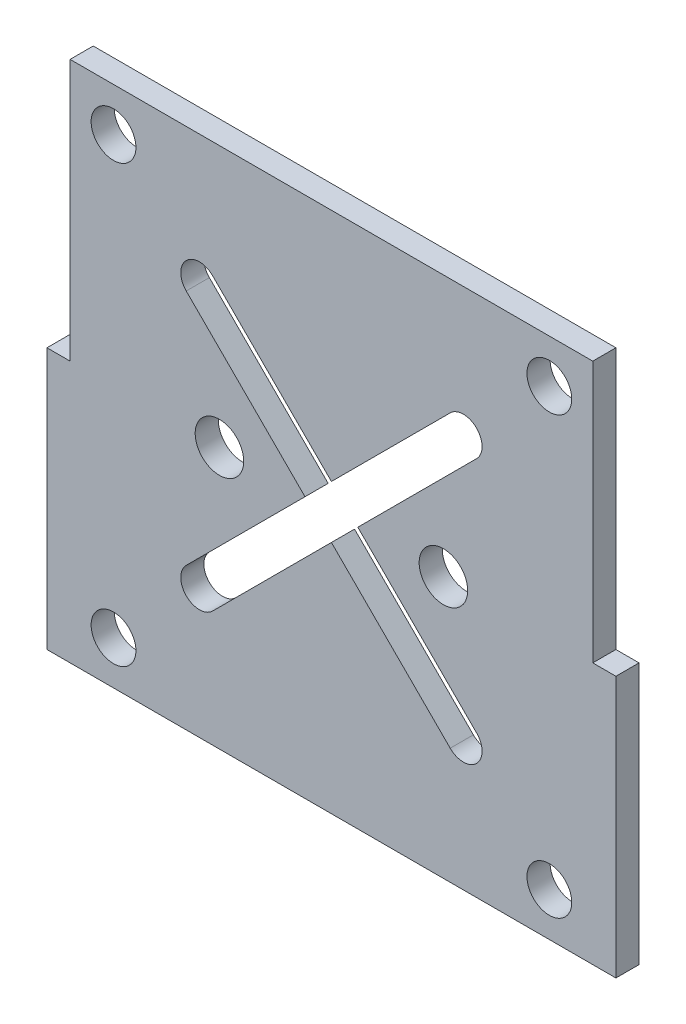
SolidWorks part; units mm, degrees
material "Teak"
ref_plane "Front Plane" through (0, 0, 0) normal (0, 0, 1) x (1, 0, 0)
ref_plane "Top Plane" through (0, 0, 0) normal (0, 1, 0) x (1, 0, 0)
ref_plane "Right Plane" through (0, 0, 0) normal (1, 0, 0) x (0, 0, -1)
sketch "Sketch1" plane through (0, 0, 0) normal (0, 0, 1) x (1, 0, 0)
  line L0 (0, 0) -> (0, 35) construction
  line L1 (-35, -35) -> (35, -35)
  line L2 (-35, -35) -> (-35, 35)
  line L3 (-35, 35) -> (35, 35)
  line L4 (35, -35) -> (35, 35)
  line L5 (-35, -35) -> (35, 35) construction
  line L6 (-35, 35) -> (35, -35) construction
  circle A0 centre (-29.1858, 29.1858) radius 3
  circle A1 centre (29.1858, 29.1858) radius 3
  circle A2 centre (29.1858, -29.1858) radius 3
  circle A3 centre (-29.1858, -29.1858) radius 3
  circle A4 centre (15, 0) radius 3.25
  circle A5 centre (-15, 0) radius 3.25
  circle A6 centre (0, 0) radius 8.1173 construction
  point P0 (0, 0)
  point P17 (0, 0)
  dimension "D3" = 6
  dimension "D7" = 20
  dimension "D8" = 6.5
  dimension "D1" = 70
  dimension "D2" = 70
  dimension "D5" = 82.55
  dimension "D6" = 0
  dimension "D4" = 4
extrude "Boss-Extrude1" add sketch "Sketch1" along normal blind 3.1
sketch "Sketch2" plane through (0, 0, 3.1) normal (0, 0, 1) x (1, 0, 0)
  line L0 (35, 0) -> (35, -35)
  line L1 (35, 0) -> (38.1, 0)
  line L2 (35, -35) -> (38.1, -35)
  line L3 (38.1, 0) -> (38.1, -35)
  line L4 (35, -35) -> (35, 35) construction
  line L5 (0, 35) -> (0, -35) construction
  line L6 (35, 35) -> (-35, 35) construction
  line L7 (-35, -35) -> (35, -35) construction
  line L8 (-38.1, 0) -> (-38.1, -35)
  line L9 (-35, -35) -> (-38.1, -35)
  line L10 (-35, 0) -> (-38.1, 0)
  line L11 (-35, 0) -> (-35, -35)
  dimension "D1" = 3.1
extrude "Boss-Extrude2" add sketch "Sketch2" against normal through all
sketch "Sketch3" plane through (0, 0, 3.1) normal (0, 0, 1) x (1, 0, 0)
  line L0 (-35, 0) -> (-35, -35) construction
  line L1 (-38.1, -35) -> (38.1, -35) construction
  line L2 (-35, -35) -> (35, 35) construction
  line L3 (35, 35) -> (35, -35) construction
  line L4 (35, -35) -> (-35, 35) construction
  line L5 (-15.9118, 19.4474) -> (-0.0019, 3.5375)
  line L6 (0, 0) -> (0, 35) construction
  line L7 (35, 35) -> (-35, 35) construction
  line L8 (-19.4474, 15.9118) -> (-3.5375, 0.0019)
  line L9 (19.4435, 15.9118) -> (3.5336, 0.0019)
  line L10 (15.908, 19.4474) -> (-0.0019, 3.5375)
  line L11 (15.908, -19.4435) -> (-0.0019, -3.5336)
  line L12 (19.4435, -15.908) -> (3.5336, 0.0019)
  line L13 (-19.4474, -15.908) -> (-3.5375, 0.0019)
  line L14 (-15.9118, -19.4435) -> (-0.0019, -3.5336)
  arc A0 (-15.9118, 19.4474) -> (-19.4474, 15.9118) centre (-17.6796, 17.6796) ccw
  arc A1 (19.4435, 15.9118) -> (15.908, 19.4474) centre (17.6757, 17.6796) ccw
  arc A2 (15.908, -19.4435) -> (19.4435, -15.908) centre (17.6757, -17.6757) ccw
  arc A3 (-19.4474, -15.908) -> (-15.9118, -19.4435) centre (-17.6796, -17.6757) ccw
  point P38 (-0.0019, 0.0019)
  dimension "D1" = 2.5
  dimension "D2" = 4
  dimension "D3" = 50
extrude "Cut-Extrude1" cut sketch "Sketch3" against normal through all
equation "\"thick\"= 3.1mm"
equation "\"small_bearing_outer\"=12.9mm"
equation "\"servo1_L\"=40.7mm"
equation "\"servo1_W\"=20.5mm"
equation "\"servo1_H\"=43.5mm"
equation "\"servo1_hL\"=49mm"
equation "\"servo1_hW\"=10mm"
equation "\"servo1_H2\"=27mm"
equation "\"large_bearing_inner\"=2.75in"
equation "\"large_bearing_outer\"=4.75in"
equation "\"large_bearing_thick\"=3/8in"
equation "\"large_bearing_h1\"=3.25in"
equation "\"large_bearing_h2\"=4.25in"
equation "\"D2@Sketch1\"=\"D1@Sketch1\""
equation "\"D5@Sketch1\"=\"large_bearing_h1\""
equation "\"D1@Boss-Extrude1\"=\"thick\""
equation "\"D1@Sketch2\"=\"thick\""
